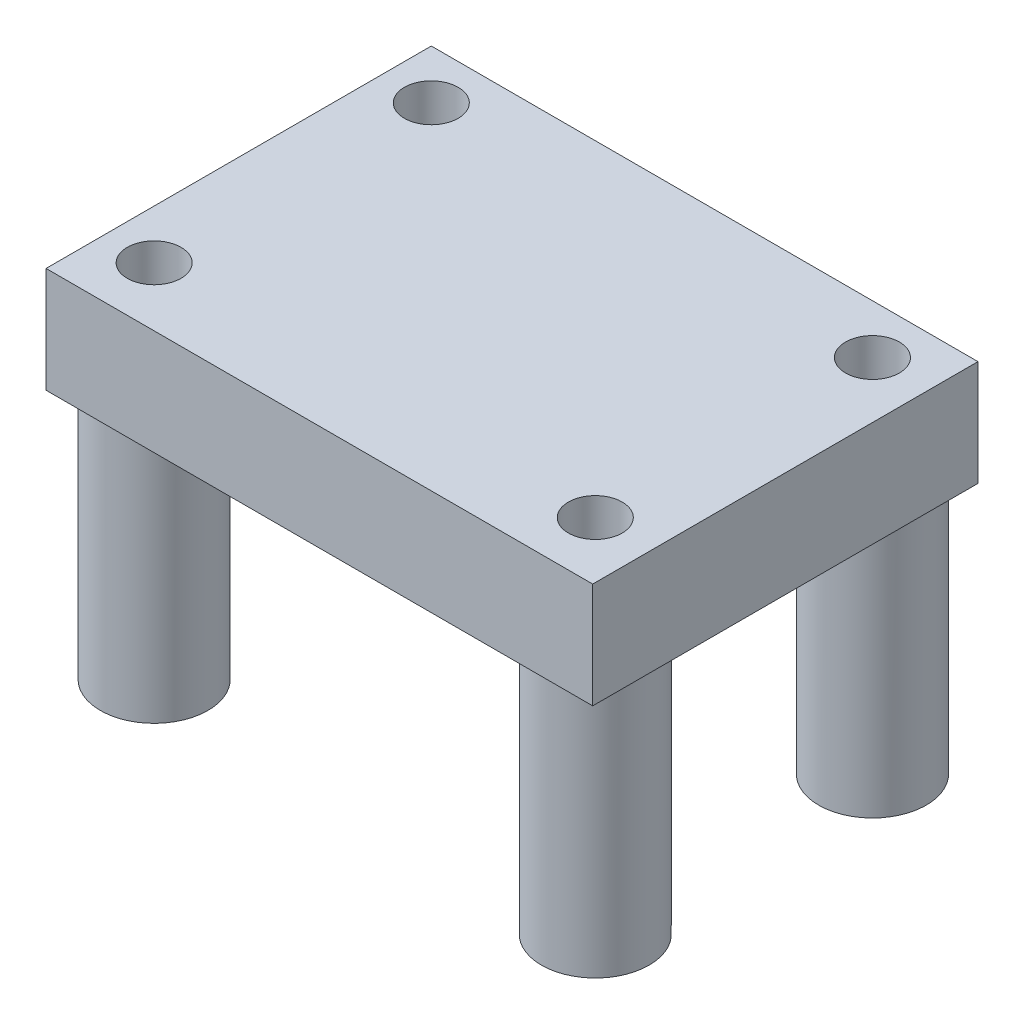
SolidWorks part; units mm, degrees
ref_plane "Front Plane" through (0, 0, 0) normal (0, 0, 1) x (1, 0, 0)
ref_plane "Top Plane" through (0, 0, 0) normal (0, 1, 0) x (1, 0, 0)
ref_plane "Right Plane" through (0, 0, 0) normal (1, 0, 0) x (0, 0, -1)
sketch "Sketch1" plane through (0, 0, 0) normal (0, 1, 0) x (1, 0, 0)
  line L1 (-16.8639, 11.4761) -> (8.5361, 11.4761)
  line L2 (-16.8639, 11.4761) -> (-16.8639, -6.4239)
  line L3 (-16.8639, -6.4239) -> (8.5361, -6.4239)
  line L4 (8.5361, 11.4761) -> (8.5361, -6.4239)
  dimension "D1" = 17.9
  dimension "D2" = 25.4
extrude "Boss-Extrude1" add sketch "Sketch1" along normal blind 4.9022
sketch "Sketch2" plane through (0, 0, 0) normal (0, -1, 0) x (1, 0, 0)
  circle A0 centre (-14.5779, 3.6877) radius 2.5
  circle A1 centre (5.9199, 3.6877) radius 2.5
  circle A2 centre (5.9199, -9.1901) radius 2.5
  circle A3 centre (-14.5779, -9.1901) radius 2.5
  dimension "D1" = 5
  dimension "D3" = 20.4978
  dimension "D6" = 5
  dimension "D9" = 5
  dimension "D12" = 5
  dimension "D2" = 12.8778
  dimension "D4" = 20.4978
  dimension "D5" = 12.8778
extrude "Boss-Extrude2" add sketch "Sketch2" along normal blind 11.8618
sketch "Sketch3" plane through (0, -11.8618, 0) normal (0, -1, 0) x (1, 0, 0)
  circle A0 centre (-14.5779, 3.6877) radius 1.25
  circle A1 centre (-14.5779, -9.1901) radius 1.25
  circle A2 centre (5.9199, -9.1901) radius 1.25
  circle A3 centre (5.9199, 3.6877) radius 1.25
  dimension "D1" = 2.5
  dimension "D2" = 2.5
  dimension "D3" = 2.5
  dimension "D4" = 2.5
extrude "Cut-Extrude1" cut sketch "Sketch3" against normal through all
